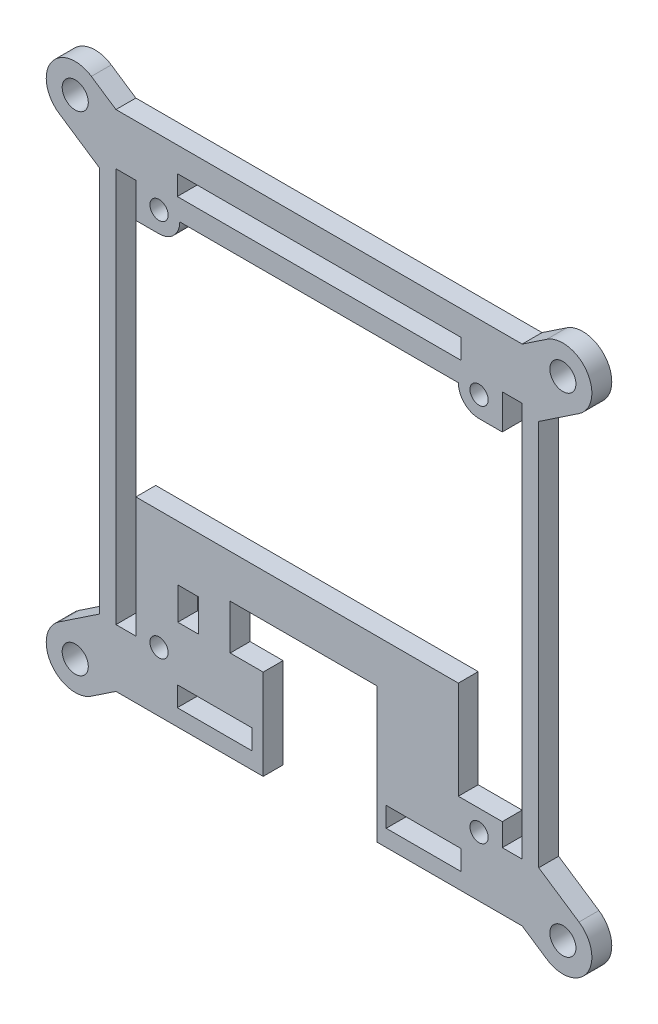
SolidWorks part; units mm, degrees
ref_plane "Front Plane" through (0, 0, 0) normal (0, 0, 1) x (1, 0, 0)
ref_plane "Top Plane" through (0, 0, 0) normal (0, 1, 0) x (1, 0, 0)
ref_plane "Right Plane" through (0, 0, 0) normal (1, 0, 0) x (0, 0, -1)
sketch "Sketch1" plane through (0, 0, 0) normal (0, 0, 1) x (1, 0, 0)
  line L3 (1.8034, 3.2766) -> (0, 3.2766) construction
  line L12 (57.9374, 3.2766) -> (59.7408, 3.2766) construction
  line L14 (57.9374, 3.2766) -> (57.9374, 63.754) construction
  line L15 (57.9374, 63.754) -> (59.7408, 63.754) construction
  line L16 (51.5874, 66.5734) -> (51.5874, 64.77) construction
  line L19 (8.1534, 66.5734) -> (8.1534, 64.77) construction
  line L20 (1.8034, 63.754) -> (-1.2446, 63.754)
  line L21 (-1.2446, 63.754) -> (-1.2446, 3.2766)
  line L22 (1.8034, 63.754) -> (1.8034, 3.2766)
  line L23 (1.8034, 3.2766) -> (-1.2446, 3.2766)
  line L24 (19.5834, -3.048) -> (19.5834, 0)
  line L25 (19.5834, -3.048) -> (8.1534, -3.048)
  line L26 (8.1534, -3.048) -> (8.1534, 0)
  line L27 (19.5834, 0) -> (8.1534, 0)
  line L28 (40.1574, -3.048) -> (40.1574, 0)
  line L29 (51.5874, -3.048) -> (40.1574, -3.048)
  line L30 (51.5874, 0) -> (40.1574, 0)
  line L31 (51.5874, -3.048) -> (51.5874, 0)
  line L32 (57.9374, 3.2766) -> (60.9854, 3.2766)
  line L33 (60.9854, 3.2766) -> (60.9854, 63.754)
  line L34 (57.9374, 3.2766) -> (57.9374, 63.754)
  line L35 (57.9374, 63.754) -> (60.9854, 63.754)
  line L36 (51.5874, 67.818) -> (51.5874, 64.77)
  line L37 (8.1534, 64.77) -> (51.5874, 64.77)
  line L38 (8.1534, 67.818) -> (51.5874, 67.818)
  line L39 (8.1534, 67.818) -> (8.1534, 64.77)
  line L40 (57.9374, 6.731) -> (51.2064, 6.731)
  line L41 (-3.7846, -5.588) -> (63.5254, -5.588)
  line L42 (-3.7846, -5.588) -> (-3.7846, 71.6116)
  line L43 (-3.7846, 71.6116) -> (63.5254, 71.6116)
  line L44 (63.5254, -5.588) -> (63.5254, 71.6116)
  line L45 (5.3594, 58.42) -> (1.8034, 58.42) construction
  line L46 (54.3814, 58.42) -> (57.9374, 58.42) construction
  line L47 (5.3594, 58.42) -> (1.8034, 58.42)
  line L48 (54.3814, 58.42) -> (57.9374, 58.42)
  line L49 (8.5344, 61.595) -> (51.2064, 61.595)
  line L50 (1.8034, 3.2766) -> (1.8034, 21.7424)
  line L51 (1.8034, 21.7424) -> (51.2064, 21.7424)
  line L52 (57.9374, 21.7424) -> (57.9374, 3.2766)
  line L53 (21.3106, -4.3434) -> (21.3106, -5.588)
  line L54 (1.8034, 21.7424) -> (1.8034, 3.2766)
  line L55 (57.9374, 21.7424) -> (57.9374, 3.2766)
  line L56 (51.2064, 6.731) -> (51.2064, 21.7424)
  line L57 (38.7858, -4.3434) -> (38.7858, -5.588)
  circle A0 centre (54.3814, 61.595) radius 1.397 construction
  circle A1 centre (5.3594, 61.595) radius 1.397 construction
  circle A2 centre (54.3814, 61.595) radius 1.397
  circle A3 centre (5.3594, 61.595) radius 1.397
  arc A8 (5.3594, 58.42) -> (5.3594, 64.77) centre (5.3594, 61.595) ccw construction
  arc A9 (54.3814, 64.77) -> (54.3814, 58.42) centre (54.3814, 61.595) ccw construction
  arc A10 (5.3594, 58.42) -> (5.3594, 64.77) centre (5.3594, 61.595) ccw
  arc A11 (54.3814, 64.77) -> (54.3814, 58.42) centre (54.3814, 61.595) ccw
  line B0 (8.2296, 13.2842) -> (11.4046, 13.2842)
  line B1 (8.2296, 13.2842) -> (8.2296, 8.3312)
  line B2 (11.4046, 13.2842) -> (11.4046, 8.3312)
  line B3 (8.2296, 8.3312) -> (11.4046, 8.3312)
  line B4 (16.256, 15.1384) -> (16.256, 8.255)
  line B5 (16.256, 8.255) -> (21.3106, 8.255)
  line B6 (38.7858, 15.1384) -> (16.256, 15.1384)
  line B7 (38.7858, -4.3434) -> (38.7858, 15.1384)
  line B8 (21.3106, 8.255) -> (21.3106, -4.3434)
  circle B9 centre (5.3594, 3.556) radius 1.397
  circle B10 centre (54.3814, 3.556) radius 1.397
  dimension "D1" = 3.048
  dimension "D2" = 6.604
  dimension "D3" = 3.048
  dimension "D4" = 6.731
  dimension "D5" = 77.1996
  dimension "D6" = 67.31
  dimension "D7" = 3.7936
sketch_block_instance "Block1-1"
sketch_block "Block1"
extrude "Boss-Extrude1" add sketch "Sketch1" along normal blind 3.048
fillet "Fillet1" radius 2.54 4 edges at (-3.7846, -5.588, 1.524) (63.5254, -5.588, 1.524) (63.5254, 71.6116, 1.524) (-3.7846, 71.6116, 1.524)
sketch "Sketch2" plane through (0, 0, 3.048) normal (0, 0, 1) x (1, 0, 0)
  line L0 (-7.48, -4.4085) -> (67.2209, -4.4085) construction
  line L1 (67.2209, -4.4085) -> (67.2209, 70.4321) construction
  line L2 (67.2209, 70.4321) -> (-7.4801, 70.4321) construction
  line L3 (-7.4801, 70.4321) -> (-7.48, -4.4085) construction
  line L4 (63.5254, 33.0118) -> (67.2208, 33.0118) construction
  line L6 (29.8704, 70.4321) -> (29.8704, 71.6116) construction
  line L8 (-5.0105, 74.1279) -> (-1.2446, 71.6116)
  line L9 (-9.9496, 66.7362) -> (-3.7846, 62.6168)
  line L11 (-5.0105, -8.1044) -> (-1.2446, -5.588)
  line L12 (-9.9496, -0.7127) -> (-3.7846, 3.4068)
  line L13 (64.7513, -8.1044) -> (60.9854, -5.588)
  line L14 (69.6904, -0.7127) -> (63.5254, 3.4068)
  line L15 (64.7513, 74.1279) -> (60.9854, 71.6116)
  line L16 (69.6904, 66.7362) -> (63.5254, 62.6168)
  line L17 (-3.7846, -3.048) -> (-3.7846, 69.0716) construction
  line L18 (63.5254, -3.048) -> (63.5254, 69.0716) construction
  line L19 (-1.2446, 71.6116) -> (60.9854, 71.6116) construction
  line L20 (-3.7846, 62.6168) -> (-3.7846, 67.9619)
  line L21 (63.5254, 62.6168) -> (63.5254, 67.9619)
  line L22 (63.5254, 3.4068) -> (63.5254, -1.9384)
  line L23 (-3.7846, 3.4068) -> (-3.7846, -1.9384)
  circle A0 centre (-7.4801, 70.4321) radius 2
  circle A1 centre (-7.48, -4.4085) radius 2
  circle A2 centre (67.2209, -4.4085) radius 2
  circle A3 centre (67.2209, 70.4321) radius 2
  circle A4 centre (-7.48, -4.4085) radius 4.445
  circle A5 centre (67.2209, -4.4085) radius 4.445
  circle A6 centre (67.2209, 70.4321) radius 4.445
  circle A7 centre (-7.4801, 70.4321) radius 4.445
  arc A8 (-1.2446, 71.6116) -> (-3.7846, 69.0716) centre (-1.2446, 69.0716) ccw construction
  arc A9 (63.5254, 69.0716) -> (60.9854, 71.6116) centre (60.9854, 69.0716) ccw construction
  arc A10 (-3.7846, -3.048) -> (-1.2446, -5.588) centre (-1.2446, -3.048) ccw construction
  arc A11 (-3.7846, -3.048) -> (-1.2446, -5.588) centre (-1.2446, -3.048) ccw
  arc A12 (60.9854, -5.588) -> (63.5254, -3.048) centre (60.9854, -3.048) ccw construction
  arc A13 (60.9854, -5.588) -> (63.5254, -3.048) centre (60.9854, -3.048) ccw
  arc A14 (63.5254, 69.0716) -> (60.9854, 71.6116) centre (60.9854, 69.0716) ccw
  arc A15 (-1.2446, 71.6116) -> (-3.7846, 69.0716) centre (-1.2446, 69.0716) ccw
  dimension "D1" = 4
  dimension "D2" = 70.7009
  dimension "D3" = 70.8406
  dimension "D4" = 8.89
extrude "Boss-Extrude2" add sketch "Sketch2" against normal up to vertex (3.048 mm away)
